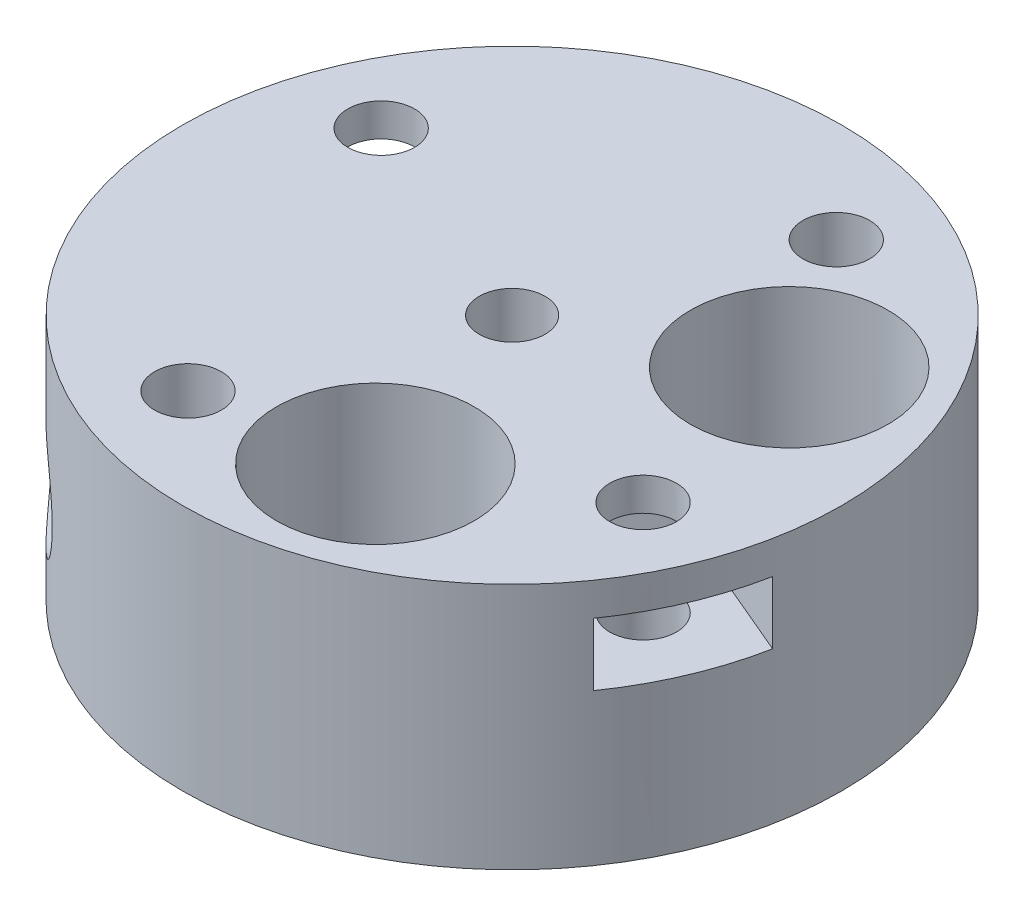
SolidWorks part; units mm, degrees
ref_plane "Front Plane" through (0, 0, 0) normal (0, 0, 1) x (1, 0, 0)
ref_plane "Top Plane" through (0, 0, 0) normal (0, 1, 0) x (1, 0, 0)
ref_plane "Right Plane" through (0, 0, 0) normal (1, 0, 0) x (0, 0, -1)
sketch "Sketch1" plane through (0, 0, 0) normal (0, 1, 0) x (1, 0, 0)
  circle A0 centre (0, 0) radius 20
  dimension "D1" = 40
extrude "Boss-Extrude1" add sketch "Sketch1" along normal mid plane 15
sketch "Sketch4" plane through (0, -7.5, 0) normal (0, -1, 0) x (1, 0, 0)
  circle A0 centre (0, 0) radius 5.125
  dimension "D1" = 10.25
extrude "Cut-Extrude2" cut sketch "Sketch4" against normal offset from surface (12.15 mm away) 2.85 up to face at (0, 7.5, 20)
sketch "Sketch5" plane through (0, 7.5, 0) normal (0, 1, 0) x (1, 0, 0)
  circle A0 centre (0, 0) radius 2
  dimension "D1" = 4
extrude "Cut-Extrude3" cut sketch "Sketch5" against normal through all both and the other way through all
sketch "Sketch15" plane through (0, -7.5, 0) normal (0, -1, 0) x (1, 0, 0)
  line L0 (0, 0) -> (0, -5.125) construction
  line L2 (-4.05, -5.125) -> (4.05, -5.125)
  line L3 (-4.05, -5.125) -> (-4.05, -3.1406)
  line L4 (-4.05, -3.1406) -> (4.05, -3.1406)
  line L5 (4.05, -5.125) -> (4.05, -3.1406)
  line L6 (0, -3.1406) -> (0, -5.125) construction
  line L7 (-4.05, -4.1328) -> (4.05, -4.1328) construction
  circle A0 centre (0, 0) radius 5.125 construction
  point P6 (0, -4.1328)
  point P10 (0, 0)
  point P11 (0, -5.125)
  dimension "D1" = 8.1
extrude "Boss-Extrude3" add sketch "Sketch15" against normal up to surface (12.15 mm away) up to face at (0, 4.65, 2)
sketch "Sketch2" plane through (0, 7.5, 0) normal (0, 1, 0) x (1, 0, 0)
  line L0 (0, 0) -> (0, 20) construction
  line L1 (0, 0) -> (-13.8076, 5.861) construction
  circle A0 centre (0, 0) radius 20 construction
  circle A1 centre (-13.8076, 5.861) radius 2.025
  dimension "D1" = 4.05
  dimension "D2" = 15
  dimension "D3" = 67
extrude "Cut-Extrude1" cut sketch "Sketch2" against normal through all
pattern_circular "CirPattern1" count 4 over 360 about axis through (0, 0, 0) along (0, 1, 0) of "Cut-Extrude1"
sketch "Sketch6" plane through (0, 0, 0) normal (0, 0, 1) x (1, 0, 0)
  line L0 (0, 7.5) -> (0, -7.5) construction
  line L1 (20, 7.5) -> (-20, 7.5) construction
  line L2 (-20, -7.5) -> (20, -7.5) construction
  line L3 (-20, 4.65) -> (20, 4.65) construction
  line L4 (-20, 7.5) -> (-20, -7.5) construction
  line L5 (20, -7.5) -> (20, 7.5) construction
  circle A0 centre (0, -1.35) radius 1.525
  dimension "D1" = 3.05
  dimension "D2" = 2.85
  dimension "D3" = 6
extrude "Cut-Extrude4" cut sketch "Sketch6" against normal through all
sketch "Sketch7" plane through (0, 0, 0) normal (0, 0, 1) x (1, 0, 0)
  circle A0 centre (0, -1.35) radius 3.25
  dimension "D1" = 6.5
extrude "Cut-Extrude5" cut sketch "Sketch7" along normal blind 8 from offset 20 offset against normal yes
sketch "Sketch9" plane through (0, 0, 0) normal (0, 0, 1) x (1, 0, 0)
  line L0 (20, -7.5) -> (20, 7.5) construction
  line L1 (0, -4.9873) -> (3.15, -3.1687) construction
  line L2 (3.15, -3.1687) -> (3.15, 0.4687)
  line L3 (3.15, 0.4687) -> (0, 2.2873)
  line L4 (0, 2.2873) -> (-3.15, 0.4687)
  line L5 (-3.15, 0.4687) -> (-3.15, -3.1687)
  line L6 (-3.15, -3.1687) -> (0, -4.9873) construction
  line L7 (3.15, -3.1687) -> (-3.15, -3.1687) construction
  line L8 (3.15, -3.1687) -> (3.15, -7.6851)
  line L9 (-3.15, -3.1687) -> (-3.15, -7.6851)
  line L10 (3.15, -7.6851) -> (-3.15, -7.6851)
  circle A0 centre (0, -1.35) radius 3.15 construction
  dimension "D1" = 6.3
extrude "Cut-Extrude11" cut sketch "Sketch9" against normal blind 2.9 from offset 6.5 offset against normal yes
pattern_circular "CirPattern2" count 2 every 135 about axis through (0, 0, 0) along (0, 1, 0) of "Cut-Extrude4", "Cut-Extrude5", "Cut-Extrude11"
sketch "Sketch8" plane through (0, 0, 0) normal (0, 1, 0) x (1, 0, 0)
  line L0 (0, 0) -> (-13.8076, 5.861) construction
  line L1 (-9.3965, 3.9886) -> (-9.9805, 8.7449)
  line L2 (-9.9805, 8.7449) -> (-14.3916, 10.6173)
  line L3 (-14.3916, 10.6173) -> (-18.2186, 7.7334) construction
  line L4 (-18.2186, 7.7334) -> (-17.6346, 2.9771) construction
  line L5 (-17.6346, 2.9771) -> (-13.2236, 1.1047)
  line L6 (-13.2236, 1.1047) -> (-9.3965, 3.9886)
  line L7 (-14.3916, 10.6173) -> (-17.6346, 2.9771) construction
  line L8 (-14.3916, 10.6173) -> (-19.5699, 12.8153)
  line L9 (-17.6346, 2.9771) -> (-22.813, 5.1751)
  line L10 (-19.5699, 12.8153) -> (-22.813, 5.1751)
  circle A0 centre (-13.8076, 5.861) radius 4.15 construction
  dimension "D1" = 8.3
extrude "Cut-Extrude7" cut sketch "Sketch8" against normal blind 3.8 from offset 5.5
pattern_circular "CirPattern3" count 2 over 360 about axis through (0, 0, 0) along (0, 1, 0) of "Cut-Extrude7"
sketch "Sketch10" plane through (0, 7.5, 0) normal (0, 1, 0) x (1, 0, 0)
  line L0 (0, 0) -> (0, -20) construction
  line L1 (0, 0) -> (3.6546, -11.9538) construction
  circle A0 centre (0, 0) radius 20 construction
  circle A1 centre (3.6546, -11.9538) radius 6
  dimension "D1" = 12
  dimension "D2" = 17
  dimension "D3" = 12.5
extrude "Cut-Extrude12" cut sketch "Sketch10" against normal through all both and the other way through all
pattern_circular "CirPattern4" count 2 every 100 about axis through (0, 7.5, 0) along (0, 1, 0) of "Cut-Extrude12"
